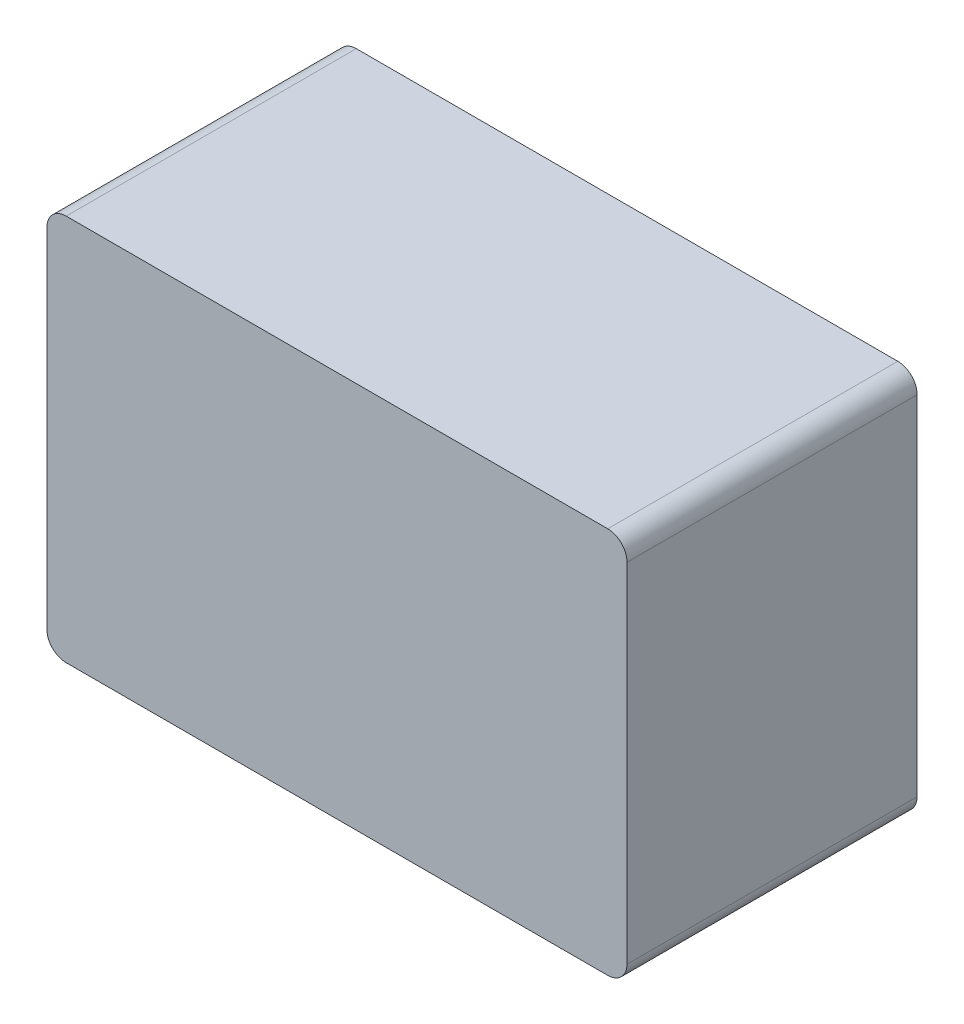
SolidWorks part; units mm, degrees
ref_plane "Front Plane" through (0, 0, 0) normal (0, 0, 1) x (1, 0, 0)
ref_plane "Top Plane" through (0, 0, 0) normal (0, 1, 0) x (1, 0, 0)
ref_plane "Right Plane" through (0, 0, 0) normal (1, 0, 0) x (0, 0, -1)
sketch "Sketch2" plane through (0, 0, 0) normal (0, 0, 1) x (1, 0, 0)
  line L1 (0, 0) -> (300, 0)
  line L2 (0, 0) -> (0, 200)
  line L3 (0, 200) -> (300, 200)
  line L4 (300, 0) -> (300, 200)
  dimension "D1" = 300
  dimension "D2" = 200
extrude "Boss-Extrude1" add sketch "Sketch2" along normal blind 150
fillet "Fillet1" radius 10 4 edges at (0, 0, 75) (300, 0, 75) (300, 200, 75) (0, 200, 75)
